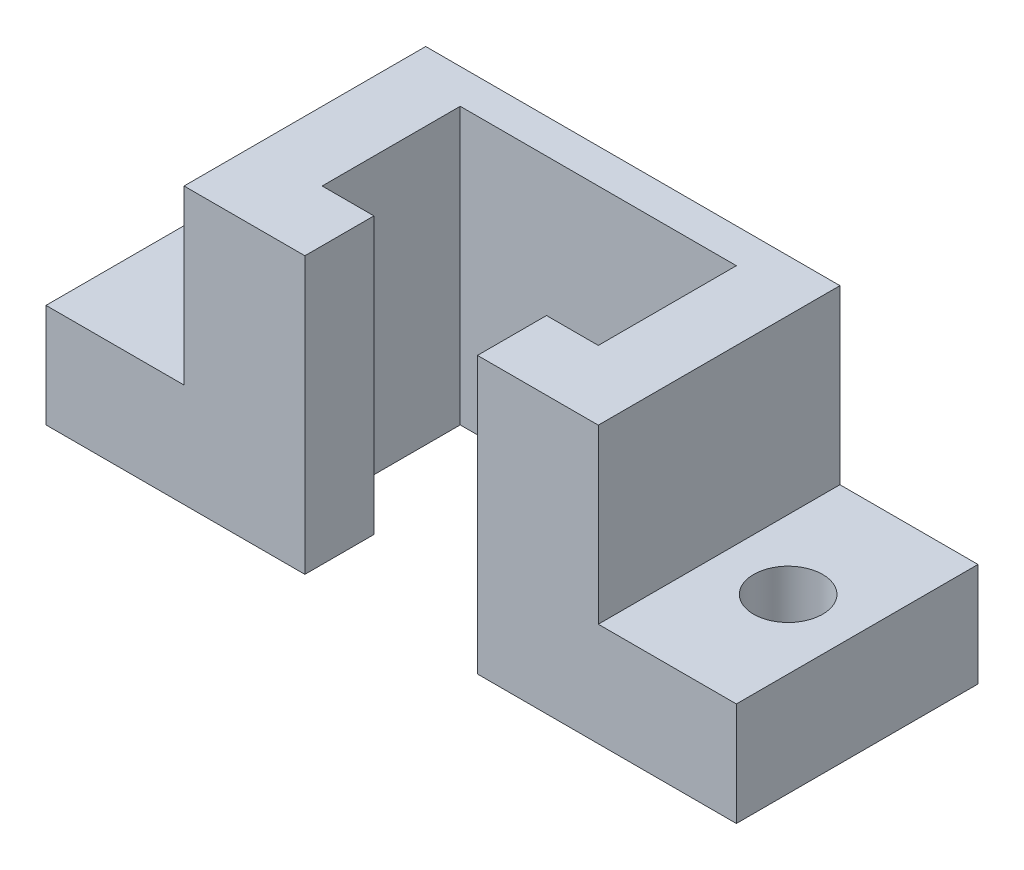
SolidWorks part; units mm, degrees
material "AISI 1020"
ref_plane "Plano frontal" through (0, 0, 0) normal (0, 0, 1) x (1, 0, 0)
ref_plane "Plano superior" through (0, 0, 0) normal (0, 1, 0) x (1, 0, 0)
ref_plane "Plano direito" through (0, 0, 0) normal (1, 0, 0) x (0, 0, -1)
sketch "Esboço1" plane through (0, 0, 0) normal (0, 0, 1) x (1, 0, 0)
  line L1 (-30, -20) -> (30, -20)
  line L2 (-30, -20) -> (-30, 20)
  line L3 (-30, 20) -> (30, 20)
  line L4 (30, -20) -> (30, 20)
  line L5 (-30, -20) -> (30, 20) construction
  line L6 (-30, 20) -> (30, -20) construction
  point P0 (0, 0)
  dimension "D1" = 40
  dimension "D2" = 60
extrude "Ressalto-extrusão1" add sketch "Esboço1" along normal blind 35
sketch "Esboço3" plane through (0, 20, 0) normal (0, 1, 0) x (1, 0, 0)
  line L0 (30, -35) -> (-30, -35) construction
  line L1 (-20, -25) -> (20, -25)
  line L2 (-20, -25) -> (-20, -5)
  line L3 (-20, -5) -> (20, -5)
  line L4 (20, -25) -> (20, -5)
  line L5 (-20, -25) -> (20, -5) construction
  line L6 (-20, -5) -> (20, -25) construction
  point P0 (0, -15)
  dimension "D1" = 40
  dimension "D2" = 20
  dimension "D3" = 0
  dimension "D4" = 10
extrude "Corte-extrusão2" cut sketch "Esboço3" against normal blind 80
sketch "Esboço4" plane through (0, 20, 0) normal (0, 1, 0) x (1, 0, 0)
  line L0 (30, -35) -> (-30, -35) construction
  line L1 (-12.5, -35) -> (12.5, -35)
  line L2 (-12.5, -35) -> (-12.5, -25)
  line L3 (-12.5, -25) -> (12.5, -25)
  line L4 (12.5, -35) -> (12.5, -25)
  line L5 (-20, -25) -> (20, -25) construction
  dimension "D1" = 25
  dimension "D2" = 12.5
extrude "Corte-extrusão3" cut sketch "Esboço4" against normal blind 80
sketch "Esboço5" plane through (30, 0, 0) normal (1, 0, 0) x (0, 0, -1)
  line L1 (0, -20) -> (0, 20) construction
  line L2 (-35, -20) -> (0, -20)
  line L3 (-35, -20) -> (-35, -5)
  line L4 (-35, -5) -> (0, -5)
  line L5 (0, -20) -> (0, -5)
  dimension "D1" = 15
extrude "Ressalto-extrusão2" add sketch "Esboço5" along normal blind 20
sketch "Esboço6" plane through (-30, 0, 0) normal (-1, 0, 0) x (0, 0, 1)
  line L1 (35, 20) -> (35, -20) construction
  line L2 (0, -20) -> (35, -20)
  line L3 (0, -20) -> (0, -5)
  line L4 (0, -5) -> (35, -5)
  line L5 (35, -20) -> (35, -5)
  dimension "D1" = 15
extrude "Ressalto-extrusão3" add sketch "Esboço6" along normal blind 20
sketch "Esboço7" plane through (0, 20, 0) normal (0, 1, 0) x (1, 0, 0)
  line L1 (-30, 0) -> (30, 0)
  line L2 (-30, 0) -> (-30, -35)
  line L3 (-30, -35) -> (30, -35)
  line L4 (30, 0) -> (30, -35)
extrude "Ressalto-extrusão4" add sketch "Esboço7" along normal blind 10
sketch "Esboço8" plane through (0, -20, 0) normal (0, -1, 0) x (1, 0, 0)
  line L6 (-50, 35) -> (-12.5, 35) construction
  line L7 (12.5, 35) -> (50, 35) construction
  line L11 (-50, 35) -> (-50, 0) construction
  line L12 (50, 0) -> (50, 35) construction
  circle A10 centre (40, 17.5) radius 5
  circle A11 centre (-40, 17.5) radius 5
  point P26 (31.25, 35)
  dimension "D2" = 10
  dimension "D3" = 10
  dimension "D8" = 17.5
  dimension "D9" = 17.5
  dimension "D12" = 10
  dimension "D13" = 10
extrude "Corte-extrusão4" cut sketch "Esboço8" against normal through all
sketch "Esboço9" plane through (0, 0, 35) normal (0, 0, 1) x (1, 0, 0)
  line L0 (-30, 30) -> (-30, -5) construction
  line L1 (30, 30) -> (-30, 30)
  line L2 (30, 30) -> (30, 19.9739)
  line L3 (30, 19.9739) -> (-30, 19.9739)
  line L4 (-30, 30) -> (-30, 19.9739)
extrude "Corte-extrusão5" cut sketch "Esboço9" against normal through all
